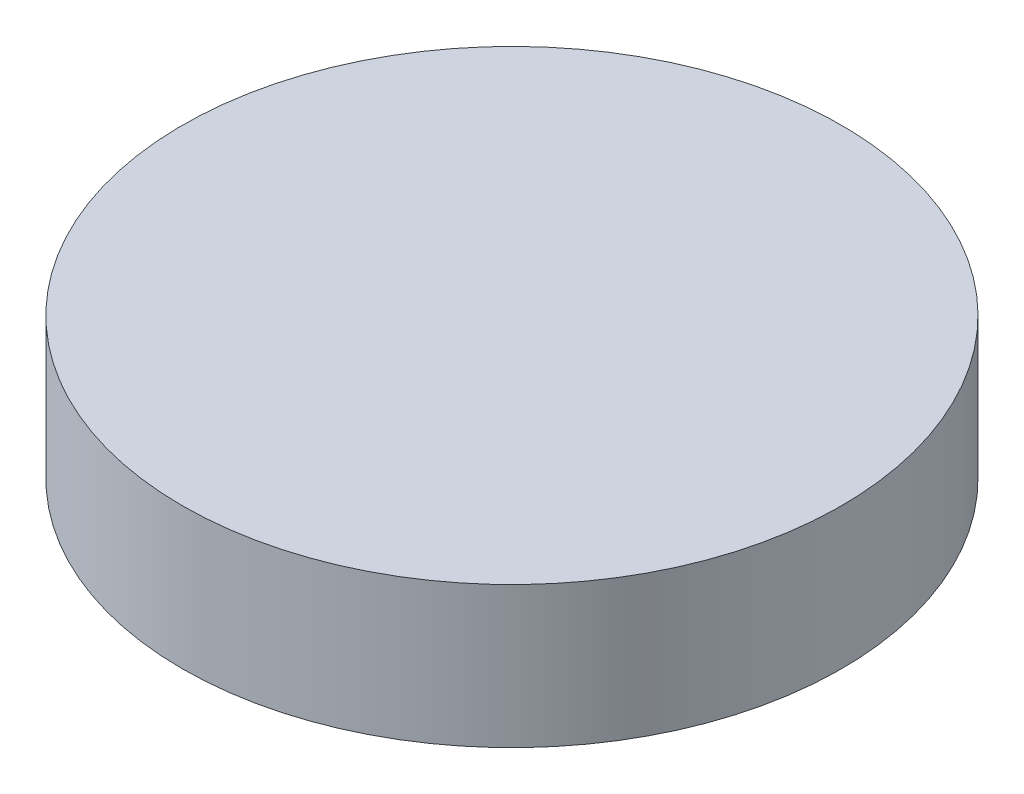
SolidWorks part; units mm, degrees
ref_plane "Front" through (0, 0, 0) normal (0, 0, 1) x (1, 0, 0)
ref_plane "Top" through (0, 0, 0) normal (0, 1, 0) x (1, 0, 0)
ref_plane "Right" through (0, 0, 0) normal (1, 0, 0) x (0, 0, -1)
sketch "Sketch1" plane through (0, 0, 0) normal (0, 1, 0) x (1, 0, 0)
  circle A0 centre (0, 0) radius 14
  dimension "D1" = 28
extrude "Boss-Extrude1" add sketch "Sketch1" along normal blind 6
